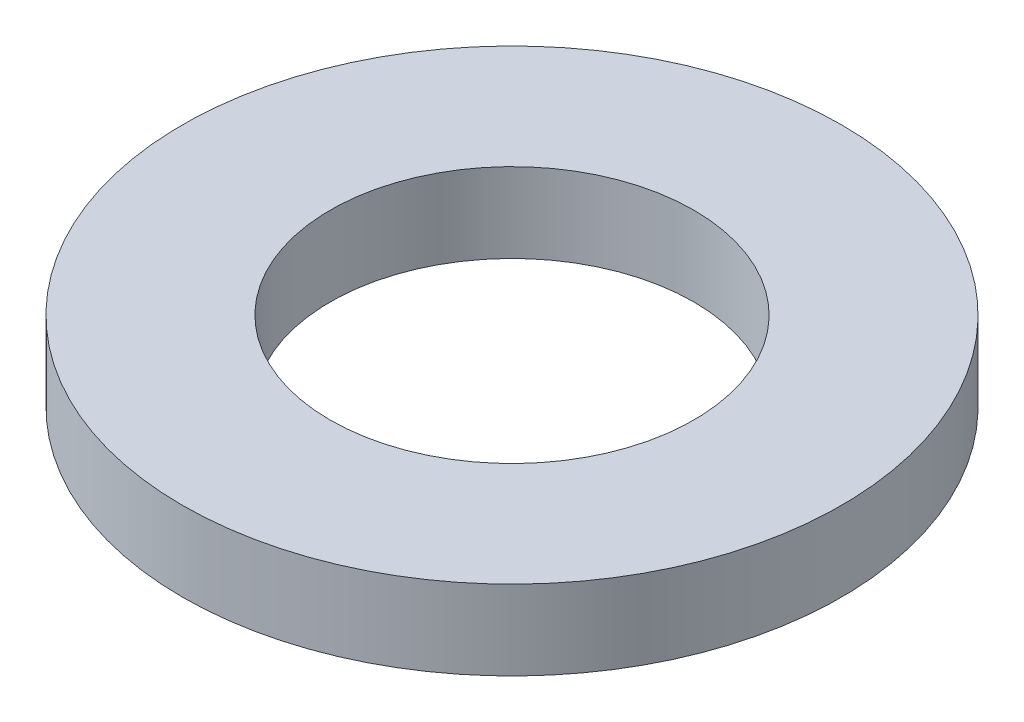
SolidWorks part; units mm, degrees
ref_plane "Front Plane" through (0, 0, 0) normal (0, 0, 1) x (1, 0, 0)
ref_plane "Top Plane" through (0, 0, 0) normal (0, 1, 0) x (1, 0, 0)
ref_plane "Right Plane" through (0, 0, 0) normal (1, 0, 0) x (0, 0, -1)
sketch "Sketch1" plane through (0, 0, 0) normal (0, 1, 0) x (1, 0, 0)
  circle A0 centre (0, 0) radius 1.6
  circle A1 centre (0, 0) radius 2.9
  dimension "D1" = 3.2
  dimension "D2" = 5.8
extrude "Boss-Extrude1" add sketch "Sketch1" along normal blind 0.7
